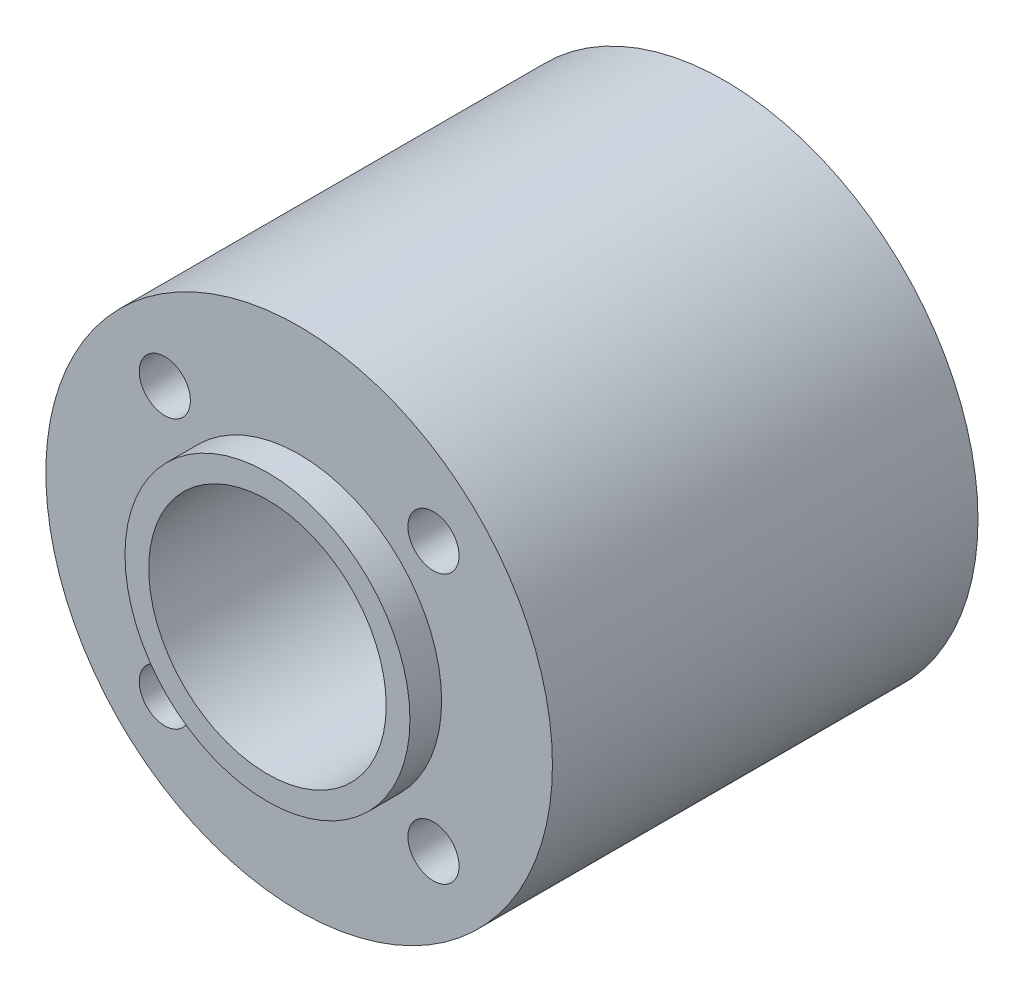
SolidWorks part; units mm, degrees
ref_plane "Front Plane" through (0, 0, 0) normal (0, 0, 1) x (1, 0, 0)
ref_plane "Top Plane" through (0, 0, 0) normal (0, 1, 0) x (1, 0, 0)
ref_plane "Right Plane" through (0, 0, 0) normal (1, 0, 0) x (0, 0, -1)
sketch "Sketch1" plane through (0, 0, 0) normal (0, 0, 1) x (1, 0, 0)
  circle A0 centre (0, 0) radius 16
  dimension "D1" = 32
extrude "Boss-Extrude1" add sketch "Sketch1" along normal blind 26.88
sketch "Sketch4" plane through (0, 0, 26.88) normal (0, 0, 1) x (1, 0, 0)
  circle A0 centre (0, 0) radius 9
  dimension "D1" = 18
extrude "Boss-Extrude2" add sketch "Sketch4" along normal blind 2
sketch "Sketch5" plane through (0, 0, 0) normal (0, 0, -1) x (-1, 0, 0)
  circle A0 centre (0, 0) radius 9
  dimension "D1" = 18
extrude "Boss-Extrude3" add sketch "Sketch5" along normal blind 2
sketch "Sketch6" plane through (0, 0, 28.88) normal (0, 0, 1) x (1, 0, 0)
  circle A0 centre (0, 0) radius 7.5
  circle A1 centre (0, 0) radius 9 construction
  dimension "D1" = 1.5
extrude "Cut-Extrude2" cut sketch "Sketch6" against normal through all
sketch "Sketch7" plane through (0, 0, 26.88) normal (0, 0, 1) x (1, 0, 0)
  line L0 (0, 13.689) -> (0, -14.9927) construction
  line L1 (0, -14.9927) -> (0, 0) construction
  line L2 (0, 0) -> (-14.901, 14.901) construction
  line L3 (-10.1, 8.485) -> (-10.1, 3.3317) construction
  circle A0 centre (-8.485, 8.485) radius 1.615
  circle A1 centre (8.485, 8.485) radius 1.615
  circle A2 centre (8.485, -8.485) radius 1.615
  circle A3 centre (-8.485, -8.485) radius 1.615
  point P18 (0, 0)
  dimension "D2" = 10.1
  dimension "D3" = 3.23
  dimension "D1" = 45
  dimension "D4" = 4
extrude "Cut-Extrude3" cut sketch "Sketch7" against normal through all
